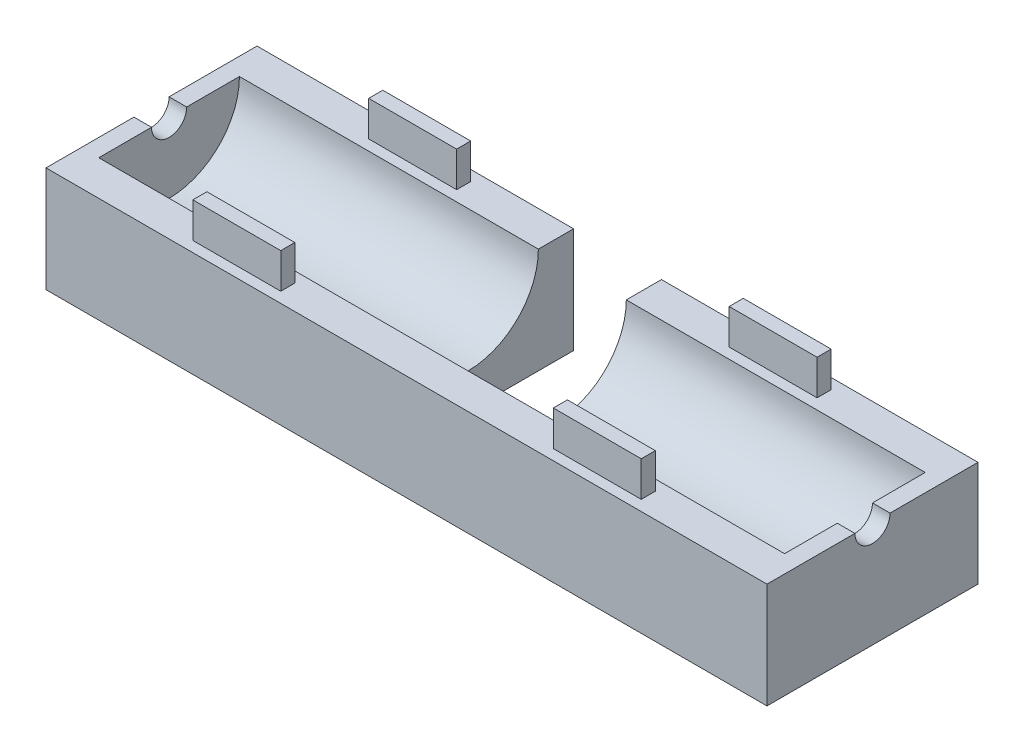
SolidWorks part; units mm, degrees
ref_plane "Front Plane" through (0, 0, 0) normal (0, 0, 1) x (1, 0, 0)
ref_plane "Top Plane" through (0, 0, 0) normal (0, 1, 0) x (1, 0, 0)
ref_plane "Right Plane" through (0, 0, 0) normal (1, 0, 0) x (0, 0, -1)
sketch "Sketch2" plane through (0, 0, 0) normal (1, 0, 0) x (0, 0, -1)
  line L0 (0, 55) -> (0, -55) construction
  line L1 (55, 0) -> (-55, 0) construction
  line L2 (-6, 6) -> (-4, 6)
  line L3 (-6, 6) -> (-6, 0)
  line L4 (-6, 0) -> (6, 0)
  line L5 (6, 6) -> (6, 0)
  line L6 (4, 6) -> (6, 6)
  arc A0 (-4, 6) -> (4, 6) centre (0, 6) ccw
  dimension "D3" = 8
  dimension "D1" = 12
  dimension "D2" = 6
  dimension "D4" = 6
  dimension "D5" = 0
extrude "Boss-Extrude2" add sketch "Sketch2" along normal mid plane 41
sketch "Sketch3" plane through (0, 6, 0) normal (0, 1, 0) x (1, 0, 0)
  line L0 (-20.5, 6) -> (-20.5, 4) construction
  line L1 (-12.75, 5.4) -> (-7.75, 5.4)
  line L2 (-12.75, 5.4) -> (-12.75, 4.6)
  line L3 (-12.75, 4.6) -> (-7.75, 4.6)
  line L4 (-7.75, 5.4) -> (-7.75, 4.6)
  line L5 (20.5, 6) -> (-20.5, 6) construction
  line L6 (-0.7754, 0) -> (-31.0154, 0) construction
  line L7 (-55, 0) -> (55, 0) construction
  line L8 (0, -3.7283) -> (0, 8.313) construction
  line L9 (0, -55) -> (0, 55) construction
  line L10 (-7.75, -5.4) -> (-7.75, -4.6)
  line L11 (-12.75, -4.6) -> (-7.75, -4.6)
  line L12 (-12.75, -5.4) -> (-12.75, -4.6)
  line L13 (-12.75, -5.4) -> (-7.75, -5.4)
  line L14 (12.75, -5.4) -> (7.75, -5.4)
  line L15 (12.75, -5.4) -> (12.75, -4.6)
  line L16 (12.75, -4.6) -> (7.75, -4.6)
  line L17 (7.75, -5.4) -> (7.75, -4.6)
  line L18 (7.75, 5.4) -> (7.75, 4.6)
  line L19 (12.75, 4.6) -> (7.75, 4.6)
  line L20 (12.75, 5.4) -> (12.75, 4.6)
  line L21 (12.75, 5.4) -> (7.75, 5.4)
  dimension "D1" = 7.75
  dimension "D2" = 0.8
  dimension "D3" = 0.6
  dimension "D4" = 5
sketch "Sketch4" plane through (0, 0, 0) normal (0, -1, 0) x (1, 0, 0)
  line L0 (55, 0) -> (-55, 0) construction
  line L1 (-2.5, 0) -> (2.5, 0)
  line L2 (-2.5, 0) -> (-2.5, -8.5007)
  line L3 (-2.5, -8.5007) -> (2.5, -8.5007)
  line L4 (2.5, 0) -> (2.5, -8.5007)
  line L5 (0, -55) -> (0, 55) construction
  dimension "D1" = 0
  dimension "D2" = 5
  dimension "D3" = 2.5
extrude "Cut-Extrude1" cut sketch "Sketch4" against normal blind 45
sketch "Sketch5" plane through (-20.5, 0, 0) normal (-1, 0, 0) x (0, 0, 1)
  line L0 (-4, 6) -> (-1, 6)
  line L1 (1, 6) -> (4, 6)
  arc A0 (-1, 6) -> (1, 6) centre (0, 6) ccw
  arc A1 (-4, 6) -> (4, 6) centre (0, 6) ccw construction
  arc A2 (-4, 6) -> (4, 6) centre (0, 6) ccw
  dimension "D1" = 2
extrude "Boss-Extrude4" add sketch "Sketch5" against normal blind 1
mirror "Mirror1" about plane through (0, 0, 0) normal (1, 0, 0) of "Boss-Extrude4"
extrude "Boss-Extrude5" add sketch "Sketch3" along normal blind 2
